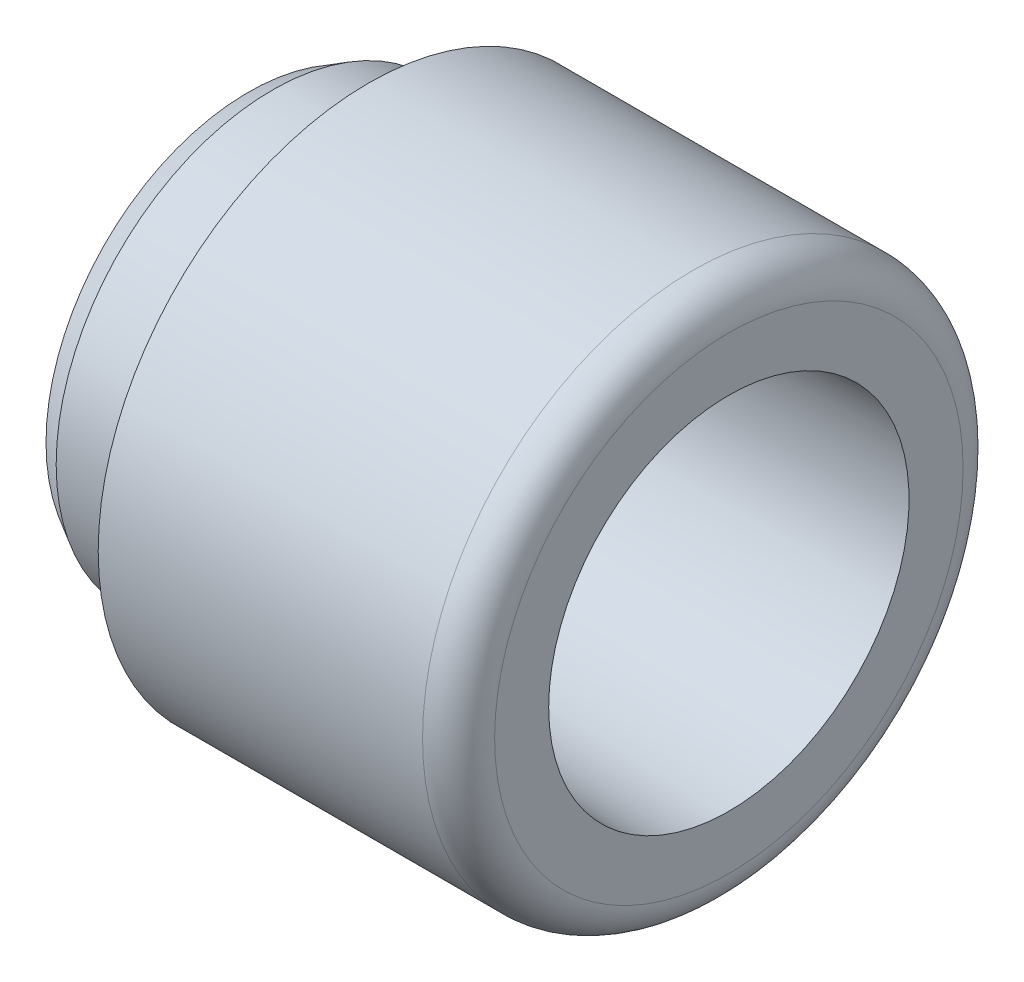
SolidWorks part; units mm, degrees
ref_plane "Plane1" through (0, 0, 0) normal (0, 0, 1) x (1, 0, 0)
ref_plane "Plane2" through (0, 0, 0) normal (0, 1, 0) x (1, 0, 0)
ref_plane "Plane3" through (0, 0, 0) normal (1, 0, 0) x (0, 0, -1)
sketch "Sketch1" plane through (0, 0, 0) normal (0, 0, 1) x (1, 0, 0)
  line L0 (0, 0) -> (80.4003, 0) construction
  line L1 (0, 16.8453) -> (2, 18)
  line L3 (40, 15) -> (40, 19.5)
  line L4 (37, 22.5) -> (10, 22.5)
  line L5 (10, 22.5) -> (10, 18)
  line L6 (10, 18) -> (2, 18)
  line L7 (0, 16.8453) -> (0, 5.1)
  line L8 (12, 13.2497) -> (12, 5.1)
  line L9 (12.7721, 14.0492) -> (40, 15)
  line L10 (0, 5.1) -> (12, 5.1)
  arc A0 (40, 19.5) -> (37, 22.5) centre (37, 19.5) ccw
  arc A1 (12, 13.2497) -> (12.7721, 14.0492) centre (12.8, 13.2497) cw
  dimension "D11" = 3
  dimension "D9" = 0.8
  dimension "D2" = 10
  dimension "D3" = 36
  dimension "D4" = 45
  dimension "D5" = 28
  dimension "D6" = 30
  dimension "D7" = 40
  dimension "D8" = 2
  dimension "D10" = 10.2
  dimension "D12" = 30
  dimension "D13" = 2
revolve "Revolve1" add sketch "Sketch1" angle 360 about L0
cosmetic thread "Cosmetic Thread1" parameters "D2"=12
